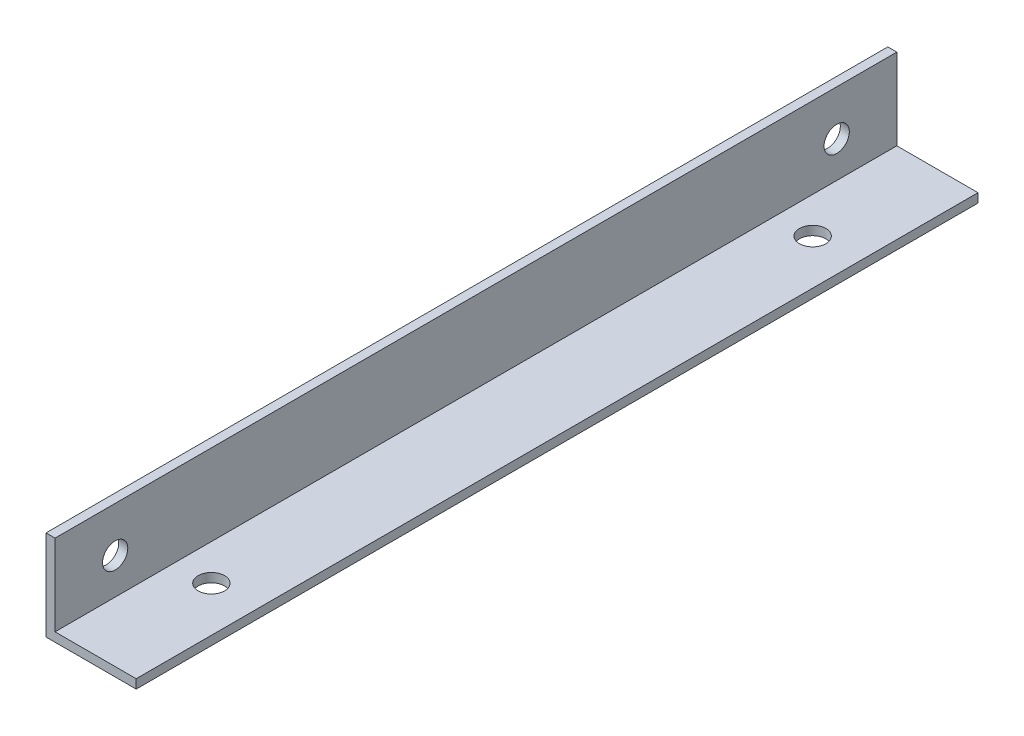
SolidWorks part; units mm, degrees
ref_plane "正面" through (0, 0, 0) normal (0, 0, 1) x (1, 0, 0)
ref_plane "平面" through (0, 0, 0) normal (0, 1, 0) x (1, 0, 0)
ref_plane "右側面" through (0, 0, 0) normal (1, 0, 0) x (0, 0, -1)
sketch "ｽｹｯﾁ1" plane through (0, 0, 0) normal (0, 0, 1) x (1, 0, 0)
  line L0 (0, 0) -> (0, 15)
  line L1 (0, 15) -> (1.5, 15)
  line L2 (1.5, 15) -> (1.5, 1.5)
  line L3 (1.5, 1.5) -> (15, 1.5)
  line L4 (15, 1.5) -> (15, 0)
  line L5 (15, 0) -> (0, 0)
  dimension "D1" = 15
  dimension "D2" = 15
  dimension "D3" = 1.5
  dimension "D4" = 1.5
extrude "ﾎﾞｽ - 押し出し1" add sketch "ｽｹｯﾁ1" along normal blind 140
sketch "ｽｹｯﾁ2" plane through (0, 0, 0) normal (-1, 0, 0) x (0, 0, 1)
  line L0 (140, 7.5) -> (130, 7.5)
  line L1 (140, 15) -> (140, 0) construction
  line L2 (0, 7.5) -> (10, 7.5)
  line L3 (0, 15) -> (0, 0) construction
  circle A0 centre (130, 7.5) radius 2.1
  circle A1 centre (10, 7.5) radius 2.1
  dimension "D3" = 4.2
  dimension "D4" = 4.2
  dimension "D1" = 10
  dimension "D2" = 10
extrude "ｶｯﾄ - 押し出し1" cut sketch "ｽｹｯﾁ2" against normal blind 140
sketch "ｽｹｯﾁ3" plane through (0, 0, 0) normal (0, -1, 0) x (-1, 0, 0)
  line L0 (-7.5, -140) -> (-7.5, -120)
  line L1 (0, -140) -> (-15, -140) construction
  line L2 (-7.5, 0) -> (-7.5, -20)
  line L3 (0, 0) -> (-15, 0) construction
  circle A0 centre (-7.5, -120) radius 2.2
  circle A1 centre (-7.5, -20) radius 2.2
  dimension "D2" = 4.4
  dimension "D4" = 4.4
  dimension "D1" = 20
  dimension "D3" = 20
extrude "ｶｯﾄ - 押し出し2" cut sketch "ｽｹｯﾁ3" against normal blind 140
